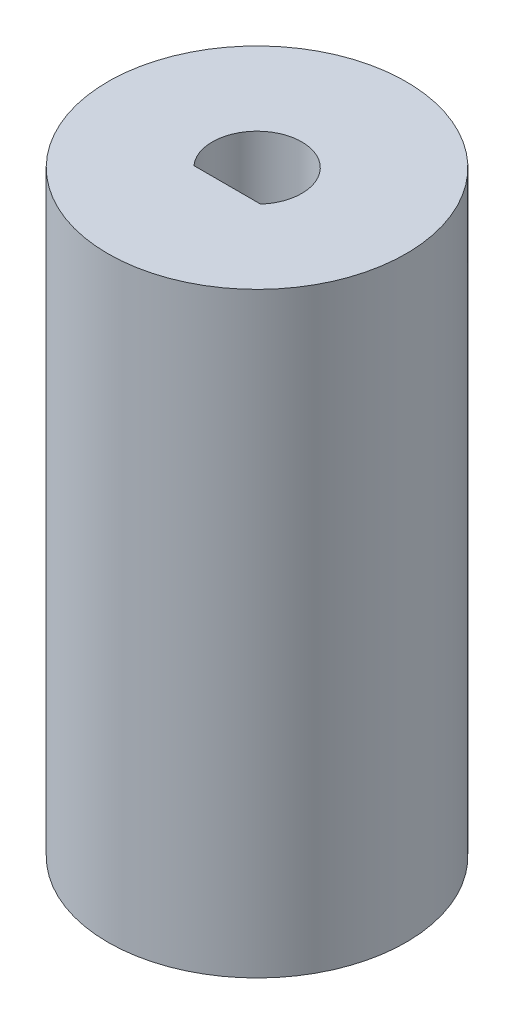
SolidWorks part; units mm, degrees
ref_plane "Ön Düzlem" through (0, 0, 0) normal (0, 0, 1) x (1, 0, 0)
ref_plane "Üst Düzlem" through (0, 0, 0) normal (0, 1, 0) x (1, 0, 0)
ref_plane "Sağ Düzlem" through (0, 0, 0) normal (1, 0, 0) x (0, 0, -1)
sketch "Sketch1" plane through (0, 0, 0) normal (0, 1, 0) x (1, 0, 0)
  circle A0 centre (0, 0) radius 10
extrude "Boss-Extrude1" add sketch "Sketch1" along normal blind 40
sketch "Sketch2" plane through (0, 40, 0) normal (0, 1, 0) x (1, 0, 0)
  line L0 (2.2361, -2) -> (-2.2361, -2)
  arc A0 (2.2361, -2) -> (-2.2361, -2) centre (0, 0) ccw
  dimension "D1" = 2
  dimension "D2" = 6
extrude "Cut-Extrude1" cut sketch "Sketch2" against normal blind 10
